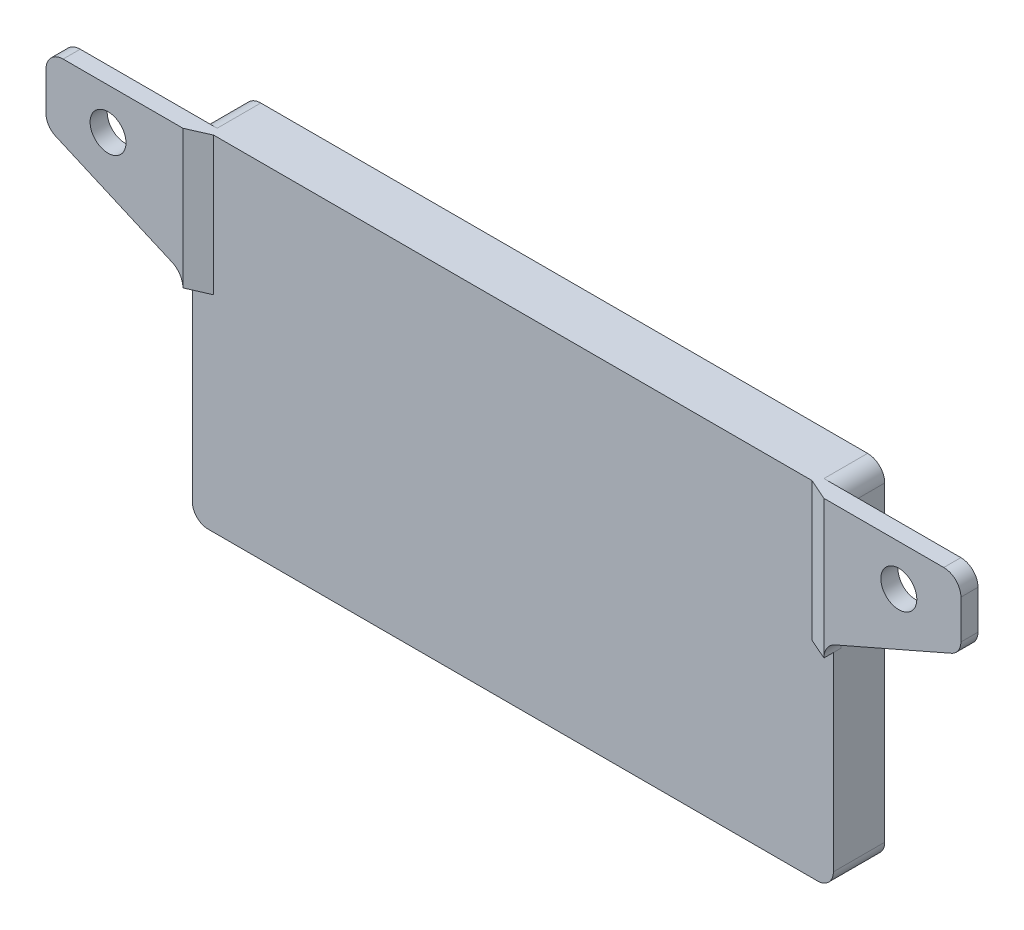
SolidWorks part; units mm, degrees
ref_plane "Front Plane" through (0, 0, 0) normal (0, 0, 1) x (1, 0, 0)
ref_plane "Top Plane" through (0, 0, 0) normal (0, 1, 0) x (1, 0, 0)
ref_plane "Right Plane" through (0, 0, 0) normal (1, 0, 0) x (0, 0, -1)
sketch "Sketch1" plane through (0, 0, 0) normal (0, 0, 1) x (1, 0, 0)
  line L0 (99.95, 149.85) -> (25.05, 149.85)
  line L1 (25.05, 148) -> (25.05, 111.5)
  line L2 (26.9, 109.65) -> (98.1, 109.65)
  line L3 (99.95, 111.5) -> (99.95, 148)
  line L4 (24.9, 148) -> (24.9, 111.5)
  line L5 (26.9, 109.5) -> (98.1, 109.5)
  line L6 (100.1, 111.5) -> (100.1, 148)
  line L7 (102.1, 150) -> (22.9, 150)
  line L8 (24.9, 148) -> (24.9, 111.5) construction
  line L9 (26.9, 109.5) -> (98.1, 109.5) construction
  line L10 (100.1, 111.5) -> (100.1, 148) construction
  line L11 (102.1, 150) -> (22.9, 150) construction
  line L12 (25.05, 148) -> (25.05, 149.85)
  line L14 (101.0046, 149.85) -> (23.9954, 149.85) construction
  line L15 (99.95, 148) -> (99.95, 149.85)
  arc A1 (25.05, 111.5) -> (26.9, 109.65) centre (26.9, 111.5) ccw
  arc A2 (98.1, 109.65) -> (99.95, 111.5) centre (98.1, 111.5) ccw
  arc A4 (24.9, 111.5) -> (26.9, 109.5) centre (26.9, 111.5) ccw
  arc A5 (98.1, 109.5) -> (100.1, 111.5) centre (98.1, 111.5) ccw
  arc A6 (102.1, 150) -> (100.1, 148) centre (102.1, 148) ccw
  arc A7 (24.9, 148) -> (22.9, 150) centre (22.9, 148) ccw
  arc A8 (24.9, 111.5) -> (26.9, 109.5) centre (26.9, 111.5) ccw construction
  arc A9 (98.1, 109.5) -> (100.1, 111.5) centre (98.1, 111.5) ccw construction
  arc A10 (102.1, 150) -> (100.1, 148) centre (102.1, 148) ccw construction
  arc A11 (24.9, 148) -> (22.9, 150) centre (22.9, 148) ccw construction
  arc A16 (25.05, 148) -> (23.9954, 149.85) centre (22.9, 148) ccw construction
  arc A17 (101.0046, 149.85) -> (99.95, 148) centre (102.1, 148) ccw construction
  dimension "D1" = 0
  dimension "D2" = 0.15
extrude "Boss-Extrude1" add sketch "Sketch1" along normal up to surface (5.1 mm away)
sketch "Sketch2" plane through (0, 0, 5.1) normal (0, 0, 1) x (1, 0, 0)
  line L24 (101.2984, 135.5243) -> (114.9016, 141.4757) construction
  line L25 (116.1, 143.308) -> (116.1, 148) construction
  line L26 (118.1, 150) -> (102.1, 150) construction
  line L28 (8.9, 148) -> (8.9, 143.308) construction
  line L29 (10.0984, 141.4757) -> (23.7016, 135.5243) construction
  line L31 (22.9, 150) -> (6.9, 150) construction
  line L32 (101.2984, 135.5243) -> (114.9016, 141.4757) construction
  line L33 (116.1, 143.308) -> (116.1, 148) construction
  line L34 (116.1, 150) -> (102.1, 150) construction
  line L36 (8.9, 148) -> (8.9, 143.308) construction
  line L37 (10.0984, 141.4757) -> (23.7016, 135.5243) construction
  line L39 (22.9, 150) -> (8.9, 150) construction
  line L40 (100.1, 111.5) -> (100.1, 133.692) construction
  line L41 (26.9, 109.5) -> (98.1, 109.5) construction
  line L42 (24.9, 133.692) -> (24.9, 111.5) construction
  line L43 (100.1, 111.5) -> (100.1, 133.692) construction
  line L44 (26.9, 109.5) -> (98.1, 109.5) construction
  line L45 (24.9, 133.692) -> (24.9, 111.5) construction
  line L46 (102.1, 150) -> (22.9, 150) construction
  line L47 (102.1, 150) -> (22.9, 150) construction
  line L48 (8.9, 148) -> (8.9, 150) construction
  line L49 (116.1, 148) -> (116.1, 150) construction
  line L50 (102.1, 149.85) -> (22.9, 149.85)
  line L51 (22.9, 149.85) -> (9.05, 149.85)
  line L52 (9.05, 148) -> (9.05, 149.85)
  line L53 (9.05, 148) -> (9.05, 143.308)
  line L54 (10.1585, 141.6131) -> (23.7618, 135.6617)
  line L55 (25.05, 133.692) -> (25.05, 111.5)
  line L56 (26.9, 109.65) -> (98.1, 109.65)
  line L57 (99.95, 111.5) -> (99.95, 133.692)
  line L58 (101.2382, 135.6617) -> (114.8415, 141.6131)
  line L59 (115.95, 143.308) -> (115.95, 148)
  line L60 (115.95, 148) -> (115.95, 149.85)
  line L61 (115.95, 149.85) -> (102.1, 149.85)
  arc A24 (114.9016, 141.4757) -> (116.1, 143.308) centre (114.1, 143.308) ccw construction
  arc A27 (101.2984, 135.5243) -> (100.1, 133.692) centre (102.1, 133.692) ccw construction
  arc A28 (8.9, 143.308) -> (10.0984, 141.4757) centre (10.9, 143.308) ccw construction
  arc A29 (24.9, 133.692) -> (23.7016, 135.5243) centre (22.9, 133.692) ccw construction
  arc A32 (114.9016, 141.4757) -> (116.1, 143.308) centre (114.1, 143.308) ccw construction
  arc A35 (101.2984, 135.5243) -> (100.1, 133.692) centre (102.1, 133.692) ccw construction
  arc A36 (8.9, 143.308) -> (10.0984, 141.4757) centre (10.9, 143.308) ccw construction
  arc A37 (24.9, 133.692) -> (23.7016, 135.5243) centre (22.9, 133.692) ccw construction
  arc A40 (98.1, 109.5) -> (100.1, 111.5) centre (98.1, 111.5) ccw construction
  arc A41 (24.9, 111.5) -> (26.9, 109.5) centre (26.9, 111.5) ccw construction
  arc A42 (98.1, 109.5) -> (100.1, 111.5) centre (98.1, 111.5) ccw construction
  arc A43 (24.9, 111.5) -> (26.9, 109.5) centre (26.9, 111.5) ccw construction
  arc A44 (9.05, 143.308) -> (10.1585, 141.6131) centre (10.9, 143.308) ccw
  arc A45 (25.05, 133.692) -> (23.7618, 135.6617) centre (22.9, 133.692) ccw
  arc A46 (25.05, 111.5) -> (26.9, 109.65) centre (26.9, 111.5) ccw
  arc A47 (98.1, 109.65) -> (99.95, 111.5) centre (98.1, 111.5) ccw
  arc A48 (101.2382, 135.6617) -> (99.95, 133.692) centre (102.1, 133.692) ccw
  arc A49 (114.8415, 141.6131) -> (115.95, 143.308) centre (114.1, 143.308) ccw
  circle A50 centre (16.3, 145.05) radius 2.1
  circle A51 centre (108.7, 145.05) radius 2.1
  dimension "D2" = 4.2
  dimension "D1" = 0.15
extrude "Boss-Extrude2" add sketch "Sketch2" along normal up to surface (0.9 mm away)
fillet "Fillet1" radius 2 4 edges at (115.95, 149.85, 5.55) (9.05, 149.85, 5.55) (25.05, 149.85, 2.55) (99.95, 149.85, 2.55)
sketch "Sketch3" plane through (0, 0, 6) normal (0, 0, 1) x (1, 0, 0)
  line L0 (99.95, 133.692) -> (99.95, 149.85)
  line L1 (11.05, 149.85) -> (113.95, 149.85) construction
  line L2 (114.8415, 141.6131) -> (101.2382, 135.6617) construction
  line L3 (115.95, 147.85) -> (115.95, 143.308) construction
  line L4 (114.8415, 141.6131) -> (101.2382, 135.6617)
  line L5 (115.95, 147.85) -> (115.95, 143.308)
  line L6 (11.05, 149.85) -> (25.05, 149.85)
  line L7 (25.05, 133.692) -> (25.05, 149.85)
  line L8 (23.7618, 135.6617) -> (10.1585, 141.6131) construction
  line L9 (9.05, 143.308) -> (9.05, 147.85) construction
  line L10 (23.7618, 135.6617) -> (10.1585, 141.6131)
  line L11 (9.05, 143.308) -> (9.05, 147.85)
  line L12 (99.95, 149.85) -> (113.95, 149.85)
  arc A0 (101.2382, 135.6617) -> (99.95, 133.692) centre (102.1, 133.692) ccw construction
  arc A1 (114.8415, 141.6131) -> (115.95, 143.308) centre (114.1, 143.308) ccw construction
  arc A2 (115.95, 147.85) -> (113.95, 149.85) centre (113.95, 147.85) ccw construction
  arc A3 (101.2382, 135.6617) -> (99.95, 133.692) centre (102.1, 133.692) ccw
  arc A4 (114.8415, 141.6131) -> (115.95, 143.308) centre (114.1, 143.308) ccw
  arc A5 (115.95, 147.85) -> (113.95, 149.85) centre (113.95, 147.85) ccw
  arc A6 (25.05, 133.692) -> (23.7618, 135.6617) centre (22.9, 133.692) ccw construction
  arc A7 (9.05, 143.308) -> (10.1585, 141.6131) centre (10.9, 143.308) ccw construction
  arc A8 (11.05, 149.85) -> (9.05, 147.85) centre (11.05, 147.85) ccw construction
  arc A9 (25.05, 133.692) -> (23.7618, 135.6617) centre (22.9, 133.692) ccw
  arc A10 (9.05, 143.308) -> (10.1585, 141.6131) centre (10.9, 143.308) ccw
  arc A11 (11.05, 149.85) -> (9.05, 147.85) centre (11.05, 147.85) ccw
  circle A12 centre (108.7, 145.05) radius 2.1 construction
  circle A13 centre (16.3, 145.05) radius 2.1 construction
  circle A14 centre (108.7, 145.05) radius 2.1
  circle A15 centre (16.3, 145.05) radius 2.1
extrude "Boss-Extrude3" add sketch "Sketch3" along normal offset from surface (1.1 mm away) 2 up to face at (17.4291, 143.8163, 5.1)
sketch "Sketch4" plane through (0, 149.85, 0) normal (0, 1, 0) x (1, 0, 0)
  line L0 (99.95, -7.1) -> (97.45, -6)
  line L1 (25.05, -6) -> (99.95, -6) construction
  line L2 (97.45, -6) -> (99.95, -6)
  line L3 (25.05, -6) -> (25.05, -7.1)
  line L4 (25.05, -7.1) -> (27.55, -6)
  line L5 (27.55, -6) -> (25.05, -6)
  line M6 (25.05, -7.1) -> (25.05, -6)
  line M7 (25.05, -6) -> (99.95, -6)
  line M8 (99.95, -6) -> (99.95, -7.1)
  dimension "D1" = 2.5
extrude "Boss-Extrude4" add sketch "Sketch4" against normal up to vertex (16.158 mm away) contours L4 M6 M7 | L0 M8 M7 up to point (25.05, 133.692, 7.1)
equation "\"width\"= 24"
equation "\"thk\"= 3"
equation "\"holesize\"= 4.2"
equation "\"holedistance\"= ( 20 + 12 ) / 2"
equation "\"threaded_hole\"= 3.9"
equation "\"fillet_radius\"= 2"
equation "\"ground_clearance\"= 25"
equation "\"tire_thk\"= 3"
equation "\"innerwheel_diam\" = \"wheel_diam\"-2*\"tire_thk\""
equation "\"innerwheel_thk\"= 8"
equation "\"wheel_diam\"= 2*(\"width\"/2+\"ground_clearance\")"
equation "\"coloursensor_holesize\"= 2.65"
equation "\"hole_to_edge\" = 4"
equation "\"M4_insert_diam\"= 5.7"
